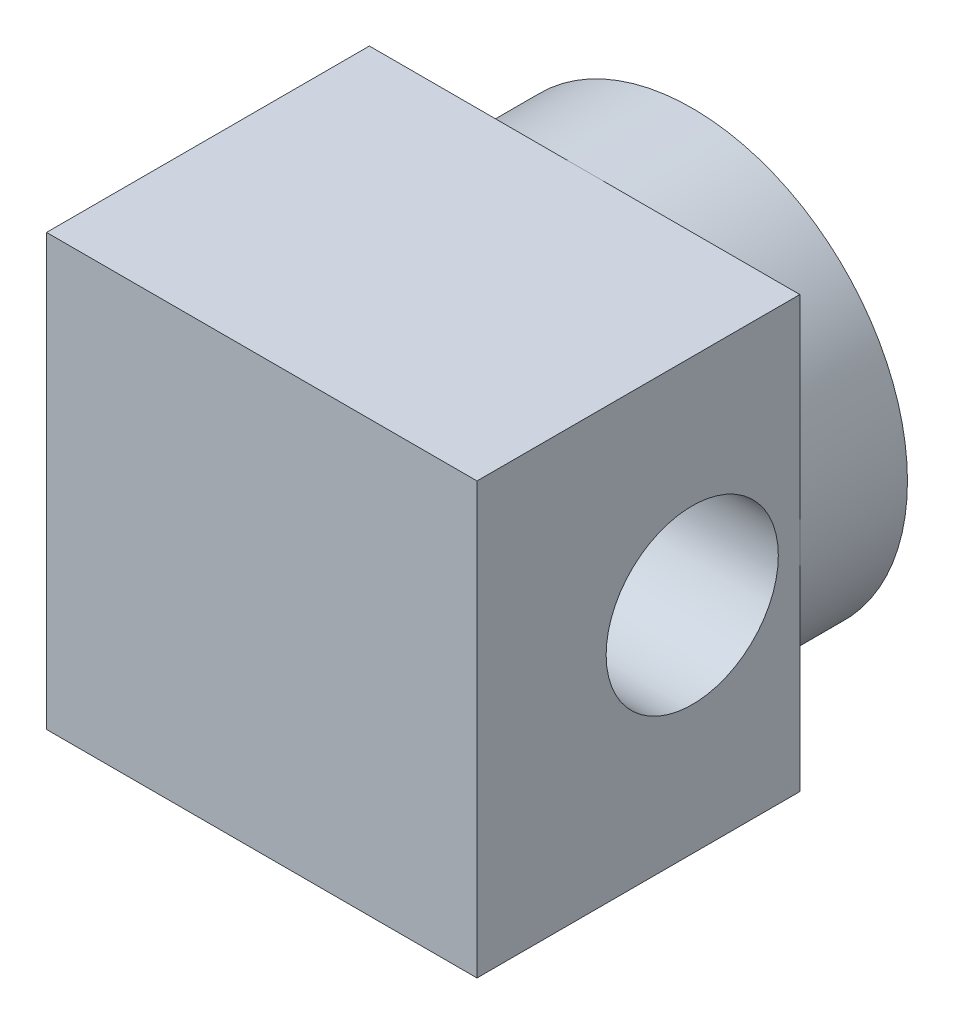
SolidWorks part; units mm, degrees
ref_plane "Front Plane" through (0, 0, 0) normal (0, 0, 1) x (1, 0, 0)
ref_plane "Top Plane" through (0, 0, 0) normal (0, 1, 0) x (1, 0, 0)
ref_plane "Right Plane" through (0, 0, 0) normal (1, 0, 0) x (0, 0, -1)
sketch "Sketch1" plane through (0, 0, 0) normal (0, 0, 1) x (1, 0, 0)
  circle A0 centre (0, 0) radius 5
  dimension "D1" = 10
extrude "Boss-Extrude1" add sketch "Sketch1" along normal blind 10
ref_plane "Plane1" through (5, 0, 0) normal (1, 0, 0) x (0, 0, -1)
ref_plane "Plane2" through (0, 0, 10) normal (0, 0, 1) x (1, 0, 0)
sketch "Sketch3" plane through (0, 0, 10) normal (0, 0, 1) x (1, 0, 0)
  line L1 (-5, 5) -> (5, 5)
  line L2 (-5, 5) -> (-5, -5)
  line L3 (-5, -5) -> (5, -5)
  line L4 (5, 5) -> (5, -5)
  line L5 (-5, 5) -> (5, -5) construction
  line L6 (-5, -5) -> (5, 5) construction
  point P0 (0, 0)
  dimension "D1" = 10
extrude "Boss-Extrude2" add sketch "Sketch3" against normal blind 7.5
sketch "Sketch2" plane through (5, 0, 0) normal (1, 0, 0) x (0, 0, -1)
  line L0 (0, 0) -> (-5, 0) construction
  circle A0 centre (-5, 0) radius 2
  dimension "D1" = 4
  dimension "D2" = 5
extrude "Cut-Extrude1" cut sketch "Sketch2" against normal through all
